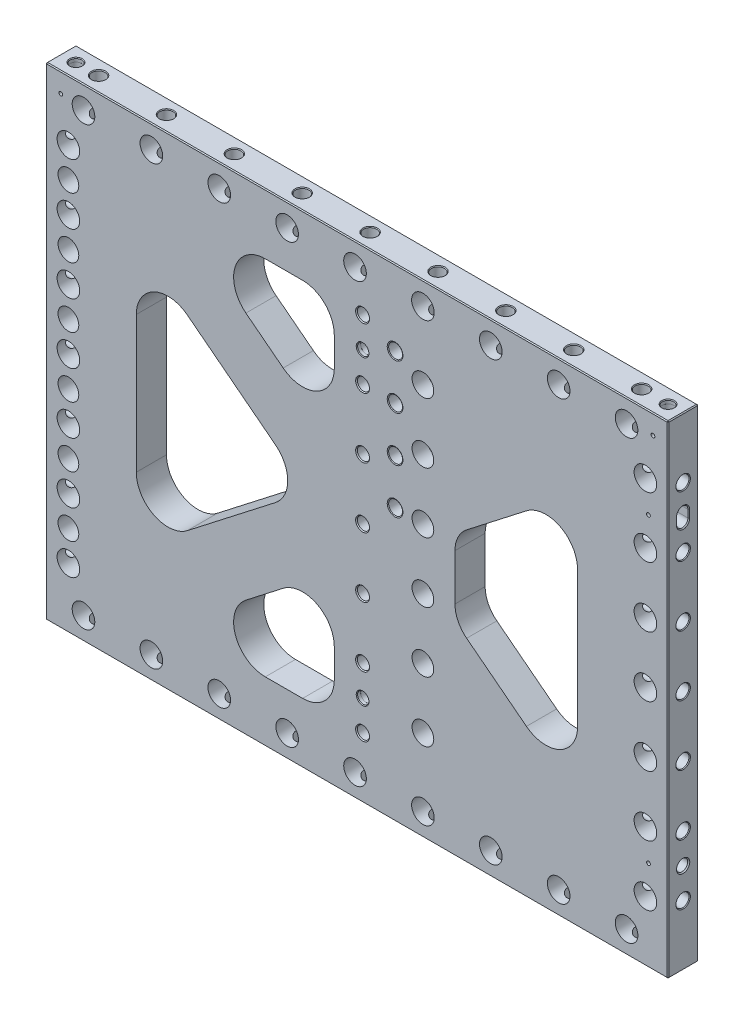
SolidWorks part; units mm, degrees
material "6061-T6 Al"
ref_plane "Front Plane" through (0, 0, 0) normal (0, 0, 1) x (1, 0, 0)
ref_plane "Top Plane" through (0, 0, 0) normal (0, 1, 0) x (1, 0, 0)
ref_plane "Right Plane" through (0, 0, 0) normal (1, 0, 0) x (0, 0, -1)
sketch "Sketch2" plane through (0, 0, 0) normal (0, 0, 1) x (1, 0, 0)
  line L0 (-261.9375, -203.2) -> (261.9375, 203.2) construction
  line L1 (-261.9375, 203.2) -> (261.9375, 203.2)
  line L2 (-261.9375, 203.2) -> (-261.9375, -203.2)
  line L3 (-261.9375, -203.2) -> (261.9375, -203.2)
  line L4 (261.9375, 203.2) -> (261.9375, -203.2)
  point P4 (0, 0)
  dimension "D1" = 523.875
  dimension "D2" = 406.4
extrude "Extrude1" add sketch "Sketch2" along normal mid plane 25.4
sketch "Sketch8" plane through (0, 0, 12.7) normal (0, 0, 1) x (1, 0, 0)
  line L0 (-261.9375, 203.2) -> (261.9375, -203.2) construction
  line L1 (261.9375, 203.2) -> (-261.9375, -203.2) construction
  line L2 (-185.7375, 111.9405) -> (-41.4392, 0)
  line L3 (-41.4392, 0) -> (-185.7375, -111.9405)
  line L4 (-185.7375, -111.9405) -> (-185.7375, 111.9405)
  line L5 (-155.0139, 152.4) -> (0, 32.1468)
  line L6 (0, 32.1468) -> (155.0139, 152.4)
  line L7 (155.0139, 152.4) -> (-155.0139, 152.4)
  line L8 (185.7375, 111.9405) -> (185.7375, -111.9405)
  line L9 (185.7375, -111.9405) -> (41.4392, 0)
  line L10 (41.4392, 0) -> (185.7375, 111.9405)
  line L11 (0, -32.1468) -> (-155.0139, -152.4)
  line L12 (-155.0139, -152.4) -> (155.0139, -152.4)
  line L13 (155.0139, -152.4) -> (0, -32.1468)
  line L14 (0, -32.1468) -> (-41.4392, 0) construction
  line L15 (-41.4392, 0) -> (0, 32.1468) construction
  line L20 (-261.9375, 203.2) -> (-261.9375, -203.2) construction
  line L21 (261.9375, 203.2) -> (-261.9375, 203.2) construction
  point P19 (-20.7196, 16.0734)
  point P23 (-20.7196, -16.0734)
  point P24 (-261.9375, 0)
  dimension "D1" = 50.8
  dimension "D2" = 76.2
  dimension "D3" = 50.8
extrude "Triangles -- Cut-Extrude2" cut sketch "Sketch8" against normal through all
fillet "Triangles -- Fillet1" radius 26.67 12 edges at (-185.7375, -111.9405, 0) (-41.4392, 0, 0) (-155.0139, -152.4, 0) (155.0139, -152.4, 0) (0, -32.1468, 0) (41.4392, 0, 0) (185.7375, -111.9405, 0) (185.7375, 111.9405, 0) (155.0139, 152.4, 0) (-155.0139, 152.4, 0) (0, 32.1468, 0) (-185.7375, 111.9405, 0)
sketch "Sketch14" plane through (0, 0, 12.7) normal (0, 0, 1) x (1, 0, 0)
  line L0 (261.9375, 203.2) -> (-261.9375, 203.2) construction
  line L1 (-19.05, 203.2) -> (19.05, 203.2)
  line L2 (-19.05, 203.2) -> (-19.05, -203.2)
  line L3 (-19.05, -203.2) -> (19.05, -203.2)
  line L4 (19.05, 203.2) -> (19.05, -203.2)
  line L5 (-261.9375, -203.2) -> (261.9375, -203.2) construction
  line L6 (19.05, 0) -> (-19.05, 0) construction
  point P10 (0, 0)
  dimension "D1" = 38.1
extrude "Extrude3" add sketch "Sketch14" against normal through all
fillet "Fillet1" radius 26.67 8 edges at (19.05, -152.4, 0) (-19.05, -152.4, 0) (-19.05, -46.925, 0) (19.05, -46.925, 0) (19.05, 46.925, 0) (19.05, 152.4, 0) (-19.05, 152.4, 0) (-19.05, 46.925, 0)
hole_wizard "3/4 (0.75) Diameter Hole1" positions "Sketch4" profile "Sketch3" hole size "3/4" standard "Ansi Inch" end condition through all
sketch "Sketch4" plane through (0, 0, 12.7) normal (0, 0, 1) x (1, 0, 0)
  line L3 (0, 0) -> (-242.8875, 0) construction
  line L6 (-261.9375, 203.2) -> (-261.9375, -203.2) construction
  point P0 (-242.8875, 0)
  dimension "D1" = 19.05
sketch "Sketch3" plane through (-242.8875, 0, 12.7) normal (1, 0, 0) x (0, -1, 0)
  line L0 (0, 0) -> (0, 25.4)
  line L1 (0, 25.4) -> (9.525, 25.4)
  line L2 (9.525, 25.4) -> (9.525, 0)
  line L5 (9.525, 0) -> (0, 0)
  line L11 (0, -6.35) -> (0, 107.95) construction
  dimension "Thru Hole Dia." = 19.05
  dimension "Thru Hole Depth" = 25.4
hole_wizard "7/16 (0.4375) Diameter Hole1" positions "Sketch6" profile "Sketch5" hole size "7/16" standard "Ansi Inch"
sketch "Sketch6" plane through (-261.9375, 0, 0) normal (-1, 0, 0) x (0, 0, 1)
  point P0 (0, 0)
sketch "Sketch5" plane through (-261.9375, 0, 0) normal (0, 1, 0) x (0, 0, 1)
  line L0 (0, 0) -> (0, 38.2635)
  line L1 (0, 38.2635) -> (5.5562, 34.925)
  line L2 (5.5562, 34.925) -> (5.5562, 0.6209)
  line L3 (5.5562, 0.6209) -> (6.096, 0)
  line L5 (6.096, 0) -> (0, 0)
  line L6 (-5.5562, 0.6209) -> (-6.096, 0) construction
  line L10 (0, 38.2635) -> (-5.5563, 34.925) construction
  line L11 (0, -6.35) -> (0, 107.95) construction
  dimension "Hole Dia." = 11.1125
  dimension "Hole Depth" = 34.925
  dimension "Near C'Sink Dia." = 12.192
  dimension "Near C'Sink Angle" = 82
  dimension "Drill Angle" = 118
pattern_linear "LPattern3" count 4 spacing 50.8 along (0, 1, 0) count 4 spacing 50.8 along (0, -1, 0) of "7/16 (0.4375) Diameter Hole1", "3/4 (0.75) Diameter Hole1"
mirror "Mirror1" about plane through (0, 0, 0) normal (1, 0, 0) of "LPattern3", "3/4 (0.75) Diameter Hole1", "7/16 (0.4375) Diameter Hole1"
hole_wizard "3/4 (0.75) Diameter Hole2" positions "Sketch11" profile "Sketch10" hole size "3/4" standard "Ansi Inch" end condition through all
sketch "Sketch11" plane through (0, 0, 12.7) normal (0, 0, 1) x (1, 0, 0)
  line L2 (-261.9375, -203.2) -> (261.9375, -203.2) construction
  point P0 (-1.5875, -184.15)
  dimension "D1" = 19.05
  dimension "D2" = 1.5875
sketch "Sketch10" plane through (-1.5875, -184.15, 12.7) normal (1, 0, 0) x (0, -1, 0)
  line L0 (0, 0) -> (0, 25.4)
  line L1 (0, 25.4) -> (9.525, 25.4)
  line L2 (9.525, 25.4) -> (9.525, 0)
  line L5 (9.525, 0) -> (0, 0)
  line L11 (0, -6.35) -> (0, 107.95) construction
  dimension "Thru Hole Dia." = 19.05
  dimension "Thru Hole Depth" = 25.4
hole_wizard "7/16 (0.4375) Diameter Hole2" positions "Sketch13" profile "Sketch12" hole size "7/16" standard "Ansi Inch"
sketch "Sketch13" plane through (0, -203.2, 0) normal (0, -1, 0) x (1, 0, 0)
  line L0 (-1.5875, -12.7) -> (-1.5875, 12.7) construction
  point P0 (-1.5875, 0)
sketch "Sketch12" plane through (-1.5875, -203.2, 0) normal (1, 0, 0) x (0, 0, -1)
  line L0 (0, 0) -> (0, 38.2635)
  line L1 (0, 38.2635) -> (5.5562, 34.925)
  line L2 (5.5562, 34.925) -> (5.5562, 0.6209)
  line L3 (5.5562, 0.6209) -> (6.096, 0)
  line L5 (6.096, 0) -> (0, 0)
  line L6 (-5.5562, 0.6209) -> (-6.096, 0) construction
  line L10 (0, 38.2635) -> (-5.5563, 34.925) construction
  line L11 (0, -6.35) -> (0, 107.95) construction
  dimension "Hole Dia." = 11.1125
  dimension "Hole Depth" = 34.925
  dimension "Near C'Sink Dia." = 12.192
  dimension "Near C'Sink Angle" = 82
  dimension "Drill Angle" = 118
pattern_linear "LPattern4" count 5 spacing 57.15 along (1, 0, 0) count 5 spacing 57.15 along (-1, 0, 0) of "7/16 (0.4375) Diameter Hole2", "3/4 (0.75) Diameter Hole2"
mirror "Mirror2" about plane through (0, 0, 0) normal (0, 1, 0) of "LPattern4"
hole_wizard "CBORE for 3/8 Socket Head Cap Screw4" positions "Sketch16" profile "Sketch15" counterbore size "3/8" standard "Ansi Inch" end condition through all
sketch "Sketch16" plane through (93.9679, 75.9436, -12.7) normal (0, 0, 1) x (1, 0, 0)
  point P1 (-89.2054, -75.9436)
  dimension "D1" = 4.7625
sketch "Sketch15" plane through (4.7625, 0, -12.7) normal (1, 0, 0) x (0, 1, 0)
  line L0 (0, 0) -> (0, 25.4)
  line L1 (5.1587, 24.614) -> (5.842, 25.4)
  line L2 (5.1587, 24.614) -> (5.1587, 10.668)
  line L3 (5.1587, 10.668) -> (8.7312, 10.668)
  line L4 (8.7312, 10.668) -> (8.7312, 0)
  line L5 (8.7312, 0) -> (0, 0)
  line L11 (0, -6.35) -> (0, 107.95) construction
  line L12 (5.842, 25.4) -> (0, 25.4)
  line L13 (-5.1587, 24.614) -> (-5.842, 25.4) construction
  dimension "Thru Hole Dia." = 10.3175
  dimension "Thru Hole Depth" = 25.4
  dimension "C'Bore Dia." = 17.4625
  dimension "C'Bore Depth" = 10.668
  dimension "Far C'Sink Dia." = 11.684
  dimension "Far C'Sink Angle" = 82
pattern_linear "LPattern5" count 4 spacing 50.8 along (0, -1, 0) count 4 spacing 50.8 along (0, 1, 0) of "CBORE for 3/8 Socket Head Cap Screw4"
hole_wizard "CBORE for 3/8 Socket Head Cap Screw1" positions "Sketch18" profile "Sketch17" counterbore size "3/8" standard "Ansi Inch" end condition through all
sketch "Sketch18" plane through (0, 0, 12.7) normal (0, 0, 1) x (1, 0, 0)
  line L6 (-261.9375, -203.2) -> (261.9375, -203.2) construction
  point P40 (-242.8875, -127)
  dimension "D1" = 76.2
sketch "Sketch17" plane through (-242.8875, -127, 12.7) normal (1, 0, 0) x (0, -1, 0)
  line L0 (0, 0) -> (0, 25.4)
  line L1 (5.1587, 24.614) -> (5.842, 25.4)
  line L2 (5.1587, 24.614) -> (5.1587, 12.7)
  line L3 (5.1587, 12.7) -> (8.7312, 12.7)
  line L4 (8.7312, 12.7) -> (8.7312, 0)
  line L5 (8.7312, 0) -> (0, 0)
  line L11 (0, -6.35) -> (0, 107.95) construction
  line L12 (5.842, 25.4) -> (0, 25.4)
  line L13 (-5.1587, 24.614) -> (-5.842, 25.4) construction
  dimension "Thru Hole Dia." = 10.3175
  dimension "Thru Hole Depth" = 25.4
  dimension "C'Bore Dia." = 17.4625
  dimension "C'Bore Depth" = 12.7
  dimension "Far C'Sink Dia." = 11.684
  dimension "Far C'Sink Angle" = 82
pattern_linear "LPattern7" count 6 spacing 50.8 along (0, 1, 0) of "CBORE for 3/8 Socket Head Cap Screw1"
sketch "Sketch19" plane through (0, 0, 12.7) normal (0, 0, 1) x (1, 0, 0)
  line L1 (62.0673, 80.296) -> (93.4706, 104.6574) construction
  line L2 (77.1234, 152.4) -> (45.72, 152.4) construction
  line L3 (19.05, 101.3686) -> (19.05, 125.73) construction
  line L4 (19.05, -125.73) -> (19.05, -101.3686) construction
  line L8 (45.72, -152.4) -> (77.1234, -152.4) construction
  line L9 (93.4706, -104.6574) -> (62.0673, -80.296) construction
  line L15 (82.55, 96.1856) -> (93.4706, 104.6574)
  line L16 (77.1234, 152.4) -> (45.72, 152.4)
  line L17 (19.05, 101.3686) -> (19.05, 125.73)
  line L18 (19.05, -125.73) -> (19.05, -101.3686)
  line L20 (45.72, -152.4) -> (77.1234, -152.4)
  line L21 (93.4706, -104.6574) -> (82.55, -96.1856)
  line L22 (19.05, 101.3686) -> (19.05, -101.3686)
  line L23 (82.55, -96.1856) -> (82.55, 96.1856)
  arc A0 (93.4706, 104.6574) -> (77.1234, 152.4) centre (77.1234, 125.73) ccw construction
  arc A4 (45.72, 152.4) -> (19.05, 125.73) centre (45.72, 125.73) ccw construction
  arc A5 (19.05, -125.73) -> (45.72, -152.4) centre (45.72, -125.73) ccw construction
  arc A6 (77.1234, -152.4) -> (93.4706, -104.6574) centre (77.1234, -125.73) ccw construction
  arc A10 (93.4706, 104.6574) -> (77.1234, 152.4) centre (77.1234, 125.73) ccw
  arc A11 (45.72, 152.4) -> (19.05, 125.73) centre (45.72, 125.73) ccw
  arc A12 (19.05, -125.73) -> (45.72, -152.4) centre (45.72, -125.73) ccw
  arc A13 (77.1234, -152.4) -> (93.4706, -104.6574) centre (77.1234, -125.73) ccw
  dimension "D1" = 63.5
extrude "Extrude4" add sketch "Sketch19" against normal through all
fillet "Fillet2" radius 25.4 2 edges at (82.55, -31.892, 0) (82.55, 31.892, 0)
hole_wizard "3/8-16 Tapped Heli-Coil Hole1" positions "Sketch23" profile "Sketch22" tap size "3/8-16" standard "Helicoil® Inch" end condition through all
sketch "Sketch23" plane through (0, 0, 12.7) normal (0, 0, 1) x (1, 0, 0)
  line L0 (32.129, 139.7) -> (32.129, 101.6) construction
  line L1 (32.129, 101.6) -> (32.129, 63.5) construction
  line L2 (32.129, 63.5) -> (32.129, 25.4) construction
  line L5 (261.9375, 203.2) -> (-261.9375, 203.2) construction
  line L6 (261.9375, -203.2) -> (261.9375, 203.2) construction
  point P1 (32.129, 25.4)
  point P4 (32.129, 63.5)
  point P7 (32.129, 101.6)
  point P10 (32.129, 139.7)
  dimension "D1" = 38.1
  dimension "D2" = 229.8085
  dimension "D3" = 63.5
sketch "Sketch22" plane through (32.129, 25.4, 12.7) normal (1, 0, 0) x (0, -1, 0)
  line L0 (0, 0) -> (0, 25.4)
  line L1 (5.0419, 24.4981) -> (6.604, 25.4)
  line L2 (5.8445, 22.86) -> (5.0419, 22.86)
  line L3 (5.0419, 22.86) -> (5.0419, 24.4981)
  line L5 (5.8445, 22.86) -> (5.8445, 0.4385)
  line L6 (5.8445, 0.4385) -> (6.604, 0)
  line L7 (6.604, 0) -> (0, 0)
  line L8 (-5.8445, 0.4385) -> (-6.604, 0) construction
  line L11 (0, -6.35) -> (0, 107.95) construction
  line L12 (6.604, 25.4) -> (0, 25.4)
  line L13 (-5.0419, 24.4981) -> (-6.604, 25.4) construction
  dimension "Thru Tap Drill Dia." = 10.0838
  dimension "Thru Tap Drill Depth" = 25.4
  dimension "Thread Major Dia." = 11.6891
  dimension "Thread Depth" = 22.86
  dimension "Near C'Sink Dia." = 13.208
  dimension "Near C'Sink Angle" = 120
  dimension "Far C'Sink Dia." = 13.208
  dimension "Far C'Sink Angle" = 120
hole_wizard "CBORE for 3/8 Socket Head Cap Screw3" positions "Sketch25" profile "Sketch24" counterbore size "3/8" standard "Ansi Inch" end condition through all
sketch "Sketch25" plane through (0, 0, 12.7) normal (0, 0, 1) x (1, 0, 0)
  line L8 (-261.9375, -203.2) -> (261.9375, -203.2) construction
  point P1 (55.5625, -127)
  dimension "D1" = 55.5625
  dimension "D2" = 76.2
sketch "Sketch24" plane through (55.5625, -127, 12.7) normal (1, 0, 0) x (0, -1, 0)
  line L0 (0, 0) -> (0, 25.4)
  line L1 (5.5562, 24.4869) -> (6.35, 25.4)
  line L2 (5.5562, 24.4869) -> (5.5563, 12.7)
  line L3 (5.5563, 12.7) -> (9.1281, 12.7)
  line L4 (9.1281, 12.7) -> (9.1281, 0)
  line L5 (9.1281, 0) -> (0, 0)
  line L11 (0, -6.35) -> (0, 107.95) construction
  line L12 (6.35, 25.4) -> (0, 25.4)
  line L13 (-5.5563, 24.4869) -> (-6.35, 25.4) construction
  dimension "Thru Hole Dia." = 11.1125
  dimension "Thru Hole Depth" = 25.4
  dimension "C'Bore Dia." = 18.2562
  dimension "C'Bore Depth" = 12.7
  dimension "Far C'Sink Dia." = 12.7
  dimension "Far C'Sink Angle" = 82
pattern_linear "LPattern6" count 6 spacing 50.8 along (0, 1, 0) of "CBORE for 3/8 Socket Head Cap Screw3"
hole_wizard "3/8 (0.376) Pin Locate1" positions "Sketch27" profile "Sketch26" hole size "3/8" standard "Ansi Inch"
sketch "Sketch27" plane through (261.9375, 0, 0) normal (1, 0, 0) x (0, 0, -1)
  line L0 (0, -101.6) -> (0, -152.4) construction
  point P0 (0, -127)
sketch "Sketch26" plane through (261.9375, -127, 0) normal (0, 1, 0) x (0, 0, -1)
  line L0 (0, 0) -> (0, 21.9192)
  line L1 (0, 21.9192) -> (4.7752, 19.05)
  line L2 (4.7752, 19.05) -> (4.7752, 0.935)
  line L3 (4.7752, 0.935) -> (5.588, 0)
  line L5 (5.588, 0) -> (0, 0)
  line L6 (-4.7752, 0.935) -> (-5.588, 0) construction
  line L10 (0, 21.9192) -> (-4.7752, 19.05) construction
  line L11 (0, -6.35) -> (0, 107.95) construction
  dimension "Hole Dia." = 9.5504
  dimension "Hole Depth" = 19.05
  dimension "Near C'Sink Dia." = 11.176
  dimension "Near C'Sink Angle" = 82
  dimension "Drill Angle" = 118
sketch "Sketch28" plane through (261.9375, 0, 0) normal (1, 0, 0) x (0, 0, -1)
  line L0 (0, 152.4) -> (0, 127) construction
  line L1 (0, 127) -> (0, 101.6) construction
  line L2 (0, 123.825) -> (0, 130.175) construction
  line L3 (4.7752, 123.825) -> (4.7752, 130.175)
  line L4 (-4.7752, 123.825) -> (-4.7752, 130.175)
  arc A0 (4.7752, 123.825) -> (-4.7752, 123.825) centre (0, 123.825) cw
  arc A1 (4.7752, 130.175) -> (-4.7752, 130.175) centre (0, 130.175) ccw
  point P10 (0, 127)
  dimension "D1" = 6.35
  dimension "D2" = 9.5504
  dimension "D3" = 4.7752
extrude "Slot Locate1" cut sketch "Sketch28" against normal blind 19.05
chamfer "Chamfer1" distance 0.762 angle 45 4 edges at (261.9375, 134.9502, 0) (261.9375, 127, 4.7752) (261.9375, 127, -4.7752) (261.9375, 119.0498, 0)
hole_wizard "3/8 (0.375) Pin + Lead-In Hole1" positions "Sketch30" profile "Sketch29" counterbore size "3/8" standard "Ansi Inch"
sketch "Sketch30" plane through (0, 203.2, 0) normal (0, 1, 0) x (-1, 0, 0)
  line L0 (261.9375, 0) -> (249.2375, 0) construction
  line L1 (261.9375, 12.7) -> (261.9375, -12.7) construction
  line L4 (-261.9375, 0) -> (-249.2375, 0) construction
  line L5 (-261.9375, 12.7) -> (-261.9375, -12.7) construction
  point P0 (-249.2375, 0)
  point P21 (249.2375, 0)
  dimension "D1" = 12.7
  dimension "D2" = 12.7
sketch "Sketch29" plane through (249.2375, 203.2, 0) normal (1, 0, 0) x (0, 0, 1)
  line L0 (0, 0) -> (0, 21.9116)
  line L1 (0, 21.9116) -> (4.7625, 19.05)
  line L2 (4.7625, 19.05) -> (4.7625, 3.175)
  line L3 (4.7625, 3.175) -> (4.7879, 3.175)
  line L5 (4.7879, 3.175) -> (4.7879, 0.6282)
  line L6 (4.7879, 0.6282) -> (5.334, 0)
  line L7 (5.334, 0) -> (0, 0)
  line L8 (-4.7879, 0.6282) -> (-5.334, 0) construction
  line L10 (0, 21.9116) -> (-4.7625, 19.05) construction
  line L11 (0, -6.35) -> (0, 107.95) construction
  dimension "Hole Dia." = 9.525
  dimension "Hole Depth" = 19.05
  dimension "C'Bore Dia." = 9.5758
  dimension "C'Bore Depth" = 3.175
  dimension "Near C'Sink Dia." = 10.668
  dimension "Near C'Sink Angle" = 82
  dimension "Drill Angle" = 118
hole_wizard "1/8 (0.125) Diameter Hole1" positions "Sketch32" profile "Sketch31" hole size "1/8" standard "Ansi Inch"
sketch "Sketch32" plane through (0, 0, 12.7) normal (0, 0, 1) x (1, 0, 0)
  line L0 (242.8875, -122.2248) -> (242.8875, -131.7752) construction
  line L1 (242.8875, 130.175) -> (242.8875, 123.825) construction
  line L4 (242.8875, -122.2248) -> (242.8875, -131.7752)
  line L5 (242.8875, 130.175) -> (242.8875, 123.825)
  line L8 (-249.2375, 184.15) -> (-249.2375, 186.69) construction
  line L11 (249.2375, 184.15) -> (249.2375, 186.69) construction
  line L14 (242.8875, 127) -> (245.4275, 127) construction
  line L17 (242.8875, -127) -> (245.4275, -127) construction
  line L18 (-244.475, 184.15) -> (-254, 184.15) construction
  line L19 (-244.475, 184.15) -> (-254, 184.15)
  line L20 (254, 184.15) -> (244.475, 184.15) construction
  line L21 (254, 184.15) -> (244.475, 184.15)
  point P0 (-249.2375, 186.69)
  point P32 (249.2375, 186.69)
  point P34 (245.4275, 127)
  point P39 (245.4275, -127)
  dimension "D1" = 2.54
sketch "Sketch31" plane through (-249.2375, 186.69, 12.7) normal (1, 0, 0) x (0, -1, 0)
  line L0 (0, 0) -> (0, 10.6059)
  line L1 (0, 10.6059) -> (1.5875, 9.652)
  line L2 (1.5875, 9.652) -> (1.5875, 0)
  line L5 (1.5875, 0) -> (0, 0)
  line L10 (0, 10.6059) -> (-1.5875, 9.652) construction
  line L11 (0, -6.35) -> (0, 107.95) construction
  dimension "Hole Dia." = 3.175
  dimension "Hole Depth" = 9.652
  dimension "Drill Angle" = 118
hole_wizard "3/8 (0.375) Pin + Lead-In Hole2" positions "Sketch34" profile "Sketch33" counterbore size "3/8" standard "Ansi Inch" end condition through all
sketch "Sketch34" plane through (0, 0, 12.7) normal (0, 0, 1) x (1, 0, 0)
  line L2 (4.7625, 127) -> (4.7625, 0) construction
  line L3 (4.7625, 0) -> (4.7625, -127) construction
  circle A0 centre (4.7625, 0) radius 5.842 construction
  point P0 (4.7625, 127)
  point P22 (4.7625, -127)
  dimension "D1" = 254
sketch "Sketch33" plane through (4.7625, 127, 12.7) normal (1, 0, 0) x (0, -1, 0)
  line L0 (0, 0) -> (0, 25.4)
  line L1 (0, 25.4) -> (4.7625, 25.4)
  line L3 (4.7625, 25.4) -> (4.7625, 3.175)
  line L4 (4.7879, 3.175) -> (4.7625, 3.175)
  line L5 (4.7879, 3.175) -> (4.7879, 0.6282)
  line L6 (4.7879, 0.6282) -> (5.334, 0)
  line L7 (5.334, 0) -> (0, 0)
  line L8 (-4.7879, 0.6282) -> (-5.334, 0) construction
  line L11 (0, -6.35) -> (0, 107.95) construction
  dimension "Thru Hole Dia." = 9.525
  dimension "Thru Hole Depth" = 25.4
  dimension "C'Bore Dia." = 9.5758
  dimension "C'Bore Depth" = 3.175
  dimension "Near C'Sink Dia." = 10.668
  dimension "Near C'Sink Angle" = 82
chamfer "Chamfer2" distance 0.762 angle 45 12 edges at (261.9375, -203.2, 0) (0, -203.2, -12.7) (0, -203.2, 12.7) (-261.9375, -203.2, 0) (-261.9375, 0, 12.7) (-261.9375, 0, -12.7) (261.9375, 0, -12.7) (261.9375, 0, 12.7) (-261.9375, 203.2, 0) (0, 203.2, -12.7) (261.9375, 203.2, 0) (0, 203.2, 12.7)
